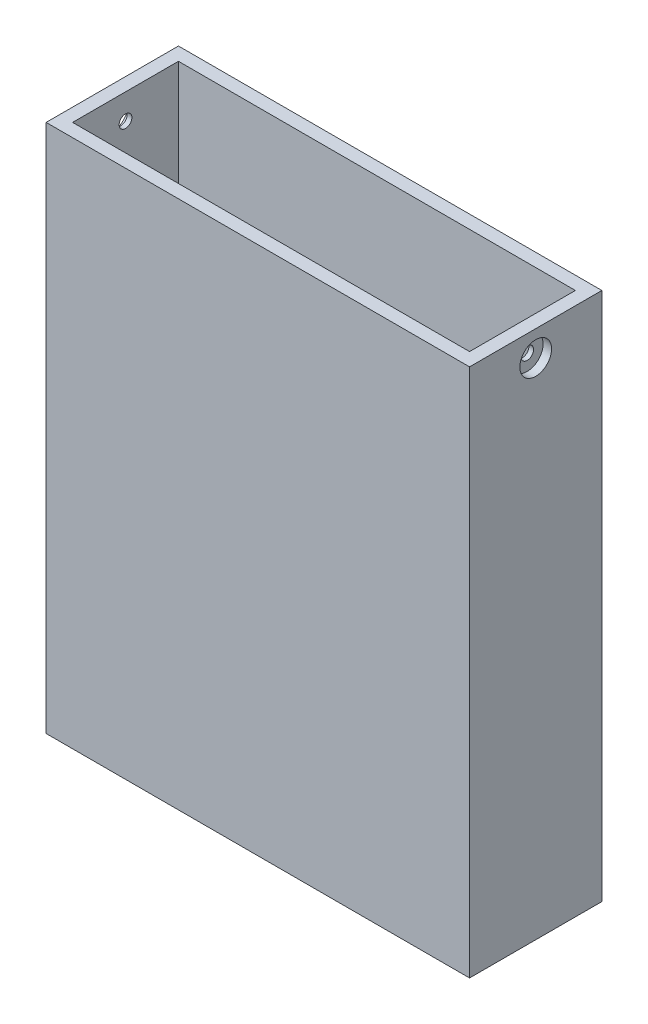
SolidWorks part; units mm, degrees
ref_plane "Front Plane" through (0, 0, 0) normal (0, 0, 1) x (1, 0, 0)
ref_plane "Top Plane" through (0, 0, 0) normal (0, 1, 0) x (1, 0, 0)
ref_plane "Right Plane" through (0, 0, 0) normal (1, 0, 0) x (0, 0, -1)
sketch "Sketch1" plane through (0, 0, 0) normal (0, 1, 0) x (1, 0, 0)
  line L1 (50.8, -15.875) -> (-50.8, -15.875)
  line L2 (50.8, -15.875) -> (50.8, 15.875)
  line L3 (50.8, 15.875) -> (-50.8, 15.875)
  line L4 (-50.8, -15.875) -> (-50.8, 15.875)
  line L5 (50.8, -15.875) -> (-50.8, 15.875) construction
  line L6 (50.8, 15.875) -> (-50.8, -15.875) construction
  point P0 (0, 0)
  dimension "D1" = 101.6
  dimension "D2" = 31.75
extrude "Boss-Extrude1" add sketch "Sketch1" along normal blind 127
sketch "Sketch2" plane through (0, 127, 0) normal (0, 1, 0) x (1, 0, 0)
  line L8 (-47.625, 12.7) -> (-47.625, -12.7)
  line L9 (-47.625, -12.7) -> (47.625, -12.7)
  line L10 (47.625, -12.7) -> (47.625, 12.7)
  line L11 (47.625, 12.7) -> (-47.625, 12.7)
  line L12 (-47.625, 12.7) -> (-47.625, -12.7)
  line L13 (-47.625, -12.7) -> (47.625, -12.7)
  line L14 (47.625, -12.7) -> (47.625, 12.7)
  line L15 (47.625, 12.7) -> (-47.625, 12.7)
  dimension "D1" = 3.175
extrude "Cut-Extrude1" cut sketch "Sketch2" against normal offset from surface (123.825 mm away) 3.175 up to face at (0, 0, 0)
sketch "Sketch3" plane through (-50.8, 0, 0) normal (-1, 0, 0) x (0, 0, 1)
  line L6 (2.3813, 119.5292) -> (2.3813, 122.2788)
  line L7 (2.3813, 122.2788) -> (0, 123.6536)
  line L8 (0, 123.6536) -> (-2.3812, 122.2788)
  line L9 (-2.3812, 122.2788) -> (-2.3812, 119.5292)
  line L10 (-2.3812, 119.5292) -> (0, 118.1544)
  line L11 (0, 118.1544) -> (2.3813, 119.5292)
  line L12 (2.3813, 119.5292) -> (2.3813, 122.2788)
  line L13 (2.3813, 122.2788) -> (0, 123.6536)
  line L14 (0, 123.6536) -> (-2.3812, 122.2788)
  line L15 (-2.3812, 122.2788) -> (-2.3812, 119.5292)
  line L16 (-2.3812, 119.5292) -> (0, 118.1544)
  line L17 (0, 118.1544) -> (2.3813, 119.5292)
  circle A0 centre (0, 57.5115) radius 2.3812 construction
  circle A1 centre (0, 57.5115) radius 1.2315
  dimension "D1" = 0
sketch "Sketch8" plane through (-50.8, 0, 0) normal (-1, 0, 0) x (0, 0, 1)
  line L0 (-2.3812, 119.5292) -> (2.3813, 122.2788) construction
  line L1 (2.3813, 119.5292) -> (-2.3812, 122.2788) construction
  line L6 (2.3813, 119.5292) -> (2.3813, 122.2788)
  line L7 (2.3813, 122.2788) -> (0, 123.6536)
  line L8 (0, 123.6536) -> (-2.3812, 122.2788)
  line L9 (-2.3812, 122.2788) -> (-2.3812, 119.5292)
  line L10 (-2.3812, 119.5292) -> (0, 118.1544)
  line L11 (0, 118.1544) -> (2.3813, 119.5292)
  line L12 (2.3813, 119.5292) -> (2.3813, 122.2788) construction
  line L13 (2.3813, 122.2788) -> (0, 123.6536) construction
  line L14 (0, 123.6536) -> (-2.3812, 122.2788) construction
  line L15 (-2.3812, 122.2788) -> (-2.3812, 119.5292) construction
  line L16 (-2.3812, 119.5292) -> (0, 118.1544) construction
  line L17 (0, 118.1544) -> (2.3813, 119.5292) construction
  point P2 (0, 120.904)
  point P4 (0, 120.904)
  point P6 (0, 120.904)
  dimension "D1" = 0
hole_wizard "CBORE for #00 Binding Head Machine Screw1" positions "Sketch9" profile "Sketch11" counterbore size "#00" standard "ANSI Inch"
sketch "Sketch9" plane through (-50.8, 0, 0) normal (-1, 0, 0) x (0, 0, 1)
  point P0 (0, 120.904)
sketch "Sketch11" plane through (-50.8, 120.904, 0) normal (0, 1, 0) x (0, 0, 1)
  line L0 (0, 0) -> (0, 101.6)
  line L1 (0, 101.6) -> (1.524, 101.6)
  line L3 (1.524, 101.6) -> (1.524, 2.032)
  line L4 (1.524, 2.032) -> (3.81, 2.032)
  line L5 (3.81, 2.032) -> (3.81, 0)
  line L7 (3.81, 0) -> (0, 0)
  line L11 (0, -6.35) -> (0, 107.95) construction
  dimension "Thru Hole Dia." = 3.048
  dimension "Thru Hole Depth" = 101.6
  dimension "C'Bore Dia." = 7.62
  dimension "C'Bore Depth" = 2.032
ref_plane "Plane1" through (0, 0, 0) normal (-1, 0, 0) x (0, 0, 1)
mirror "Mirror1" about plane through (0, 0, 0) normal (-1, 0, 0) of "CBORE for #00 Binding Head Machine Screw1"
